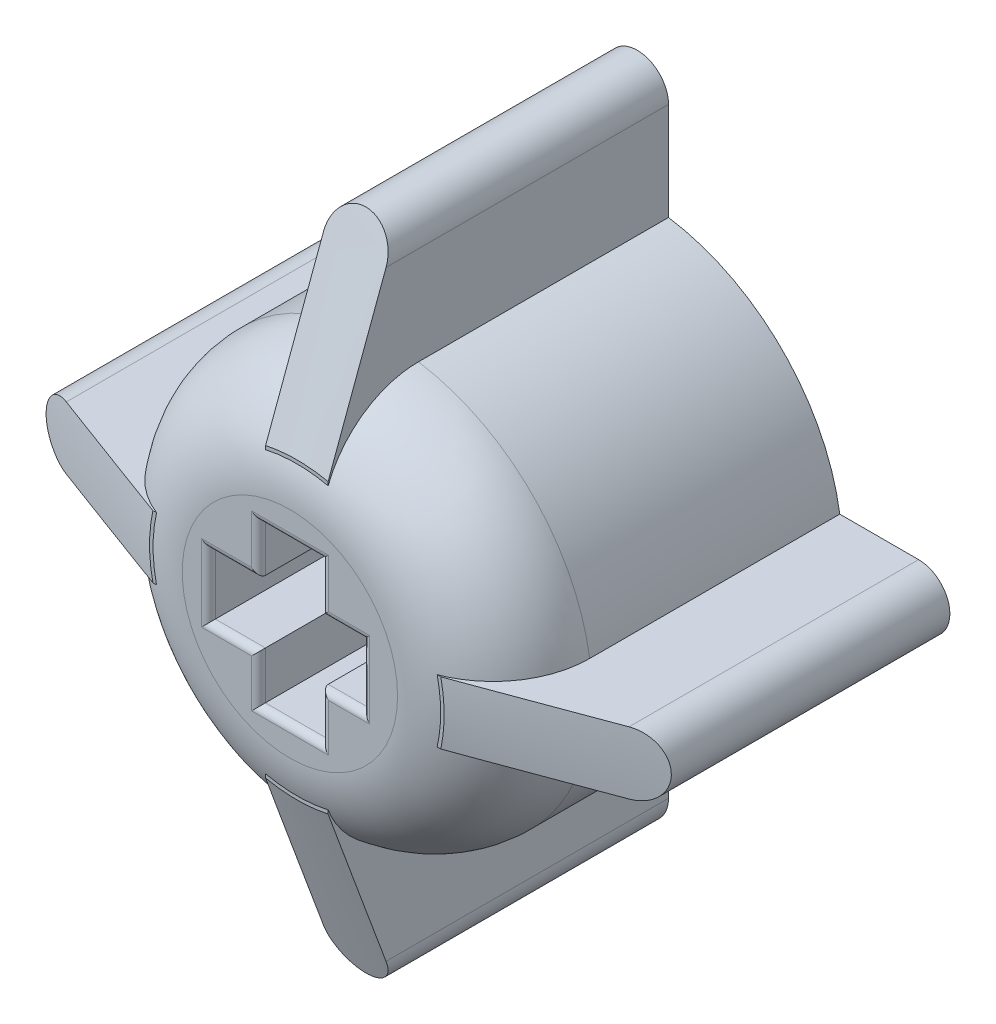
SolidWorks part; units mm, degrees
material "PVC Rigid"
ref_plane "Front Plane" through (0, 0, 0) normal (0, 0, 1) x (1, 0, 0)
ref_plane "Top Plane" through (0, 0, 0) normal (0, 1, 0) x (1, 0, 0)
ref_plane "Right Plane" through (0, 0, 0) normal (1, 0, 0) x (0, 0, -1)
sketch "Sketch1" plane through (0, 0, 0) normal (0, 0, 1) x (1, 0, 0)
  circle A0 centre (0, 0) radius 5.9
  dimension "D1" = 11.8
extrude "Extrude1" add sketch "Sketch1" against normal blind 10
fillet "Fillet1" radius 2.8 1 edges at (5.9, 0, 0)
sketch "Sketch2" plane through (0, 0, 0) normal (0, 0, 1) x (1, 0, 0)
  line L0 (-0.905, 2.315) -> (0.905, 2.315)
  line L1 (0.905, 2.315) -> (0.905, 0.905)
  line L2 (0.905, 0.905) -> (2.0935, 0.905)
  line L3 (2.0935, 0.905) -> (2.0935, -0.905)
  line L4 (2.0935, -0.905) -> (0.905, -0.905)
  line L5 (0.905, -0.905) -> (0.905, -2.2735)
  line L6 (0.905, -2.2735) -> (-0.905, -2.2735)
  line L7 (-0.905, -2.2735) -> (-0.905, -0.905)
  line L8 (-0.905, -0.905) -> (-2.3455, -0.905)
  line L9 (-2.3455, -0.905) -> (-2.3455, 0.905)
  line L10 (-2.3455, 0.905) -> (-0.905, 0.905)
  line L11 (-0.905, 0.905) -> (-0.905, 2.315)
  dimension "D1" = 1.81
  dimension "D2" = 1.41
  dimension "D3" = 0.905
  dimension "D4" = 0.905
extrude "Extrude2" cut sketch "Sketch2" against normal blind 8
fillet "Fillet2" radius 0.2 12 edges at (-1.6253, 0.905, 0) (-2.3455, 0, 0) (-1.6253, -0.905, 0) (-0.905, -1.5893, 0) (0, -2.2735, 0) (0.905, -1.5893, 0) (1.4992, -0.905, 0) (2.0935, 0, 0) (1.4992, 0.905, 0) (0.905, 1.61, 0) (0, 2.315, 0) (-0.905, 1.61, 0)
sketch "Sketch3" plane through (0, 0, -10) normal (0, 0, -1) x (-1, 0, 0)
  line L1 (-3.1962, 0.9) -> (-8.1, 0.9)
  line L2 (-3.1962, 0.9) -> (-3.1962, -0.9)
  line L3 (-3.1962, -0.9) -> (-8.1, -0.9)
  line L5 (0.9, 3.3763) -> (-0.9, 3.3763)
  line L6 (0.9, 3.3763) -> (0.9, 8.65)
  line L8 (-0.9, 3.3763) -> (-0.9, 8.65)
  line L9 (3.3403, 0.9) -> (8.1, 0.9)
  line L10 (3.3403, 0.9) -> (3.3403, -0.9)
  line L11 (3.3403, -0.9) -> (8.1, -0.9)
  line L13 (-0.9, -3.3583) -> (0.9, -3.3583)
  line L14 (-0.9, -3.3583) -> (-0.9, -8.65)
  line L16 (0.9, -3.3583) -> (0.9, -8.65)
  arc A0 (8.1, -0.9) -> (8.1, 0.9) centre (8.1, 0) ccw
  arc A1 (0.9, 8.65) -> (-0.9, 8.65) centre (0, 8.65) ccw
  arc A2 (-8.1, 0.9) -> (-8.1, -0.9) centre (-8.1, 0) ccw
  arc A3 (-0.9, -8.65) -> (0.9, -8.65) centre (0, -8.65) ccw
  dimension "D1" = 1.8
  dimension "D2" = 8.1
  dimension "D3" = 8.1
  dimension "D4" = 8.65
  dimension "D5" = 8.65
extrude "Extrude3" add sketch "Sketch3" against normal blind 9.8
ref_axis "Axis2" through (0, 0, -10.5025) along (0, 0, 1)
sketch "Sketch6" plane through (0, 0, 0) normal (1, 0, 0) x (0, 0, -1)
  line L3 (2.3185, -9.9005) -> (-0.0499, -9.9005)
  line L4 (0.1236, -4.0369) -> (2.3185, -9.9005)
  line L5 (-0.0499, -9.9005) -> (0.1236, -4.0369)
revolve "Cut-Revolve3" cut sketch "Sketch6" angle 360 about axis through (0, 0, -10.5025) along (0, 0, 1)
